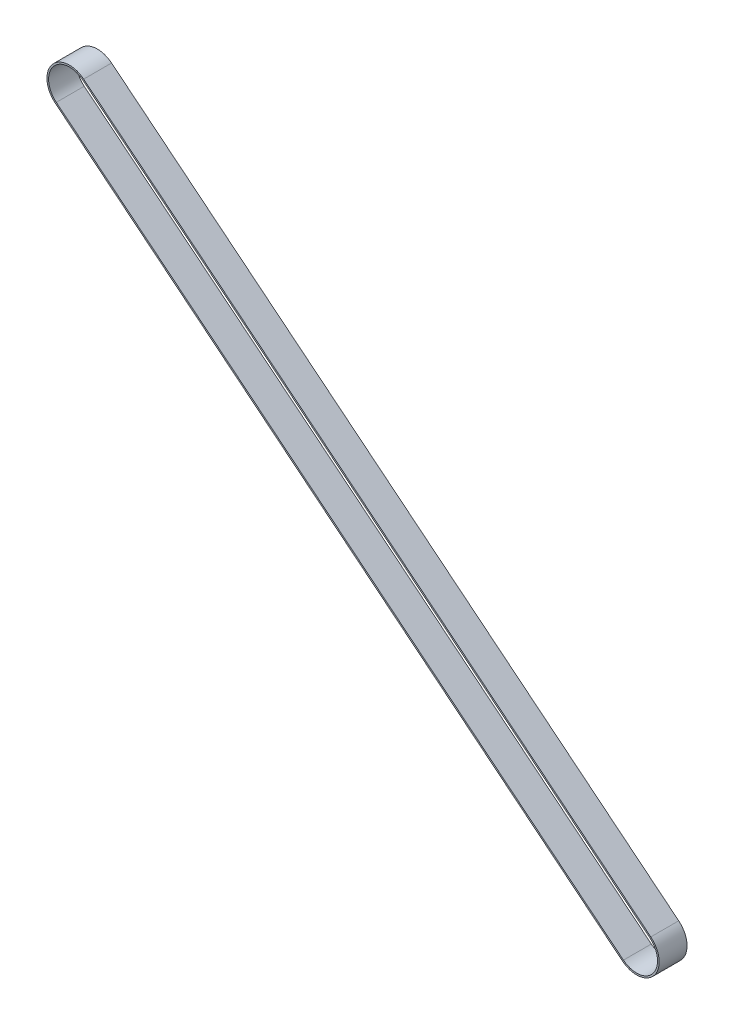
SolidWorks part; units mm, degrees
ref_plane "前视基准面" through (0, 0, 0) normal (0, 0, 1) x (1, 0, 0)
ref_plane "上视基准面" through (0, 0, 0) normal (0, 1, 0) x (1, 0, 0)
ref_plane "右视基准面" through (0, 0, 0) normal (1, 0, 0) x (0, 0, -1)
other "Configuration Table"
sketch "草图2" plane through (0, 0, 0) normal (0, 0, 1) x (1, 0, 0)
  line L0 (0, 0) -> (1, 0) construction
  line L1 (0, 0) -> (0, 1) construction
  line L2 (2.8321, 3.4971) -> (124.8321, -95.3029)
  line L3 (119.1679, -102.2971) -> (-2.8321, -3.4971)
  arc A0 (-2.8321, -3.4971) -> (2.8321, 3.4971) centre (0, 0) cw
  arc A1 (124.8321, -95.3029) -> (119.1679, -102.2971) centre (122, -98.8) cw
extrude "拉伸-薄壁1" add sketch "草图2" along normal mid plane 6 thin thin type one direction wall 0.35
